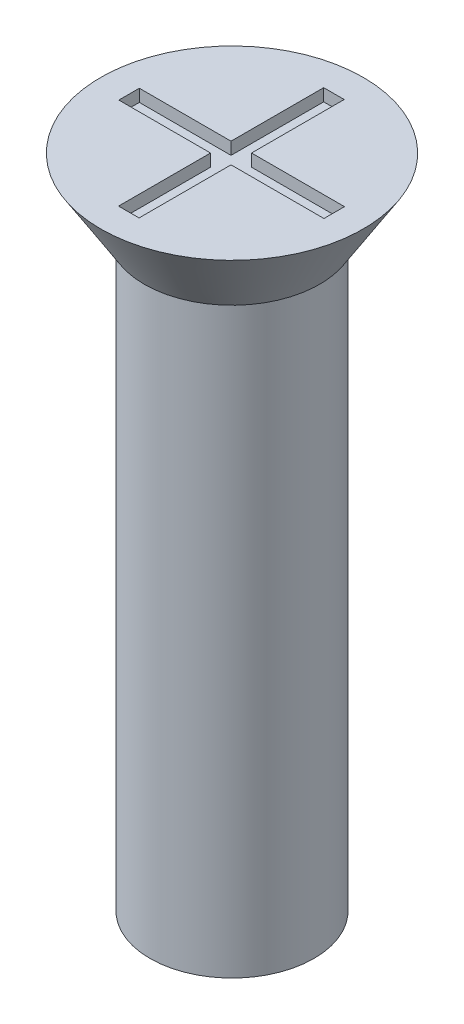
SolidWorks part; units mm, degrees
material "AISI 304"
ref_plane "Front" through (0, 0, 0) normal (0, 0, 1) x (1, 0, 0)
ref_plane "Top" through (0, 0, 0) normal (0, 1, 0) x (1, 0, 0)
ref_plane "Right" through (0, 0, 0) normal (1, 0, 0) x (0, 0, -1)
sketch "Sketch1" plane through (0, 0, 0) normal (0, 1, 0) x (1, 0, 0)
  circle A0 centre (0, 0) radius 2
  dimension "D1" = 4
extrude "Boss-Extrude1" add sketch "Sketch1" along normal blind 16
sketch "Sketch2" plane through (0, 16, 0) normal (0, 1, 0) x (1, 0, 0)
  circle A0 centre (0, 0) radius 3.2
  dimension "D1" = 6.4
extrude "Boss-Extrude2" add sketch "Sketch2" against normal blind 1.7 draft 32
sketch "Sketch3" plane through (0, 16, 0) normal (0, 1, 0) x (1, 0, 0)
  line L1 (-2.5, 0.2416) -> (2.5, 0.2416)
  line L2 (-2.5, 0.2416) -> (-2.5, -0.2584)
  line L3 (-2.5, -0.2584) -> (2.5, -0.2584)
  line L4 (2.5, 0.2416) -> (2.5, -0.2584)
  line L5 (-0.2653, 2.5) -> (0.2347, 2.5)
  line L6 (-0.2653, 2.5) -> (-0.2653, -2.5)
  line L7 (-0.2653, -2.5) -> (0.2347, -2.5)
  line L8 (0.2347, 2.5) -> (0.2347, -2.5)
  circle A0 centre (0, 0) radius 3.2 construction
  dimension "D1" = 0.5
  dimension "D2" = 0.5
  dimension "D3" = 5
  dimension "D4" = 5
  dimension "D5" = 2.5
  dimension "D6" = 2.5
extrude "Cut-Extrude1" cut sketch "Sketch3" against normal blind 0.3 contours L8 L5 L6 L1 | L8 L3 L6 L7 | L6 L1 L2 L3 | L1 L8 L3 L4 | L8 L1 L6 L3
